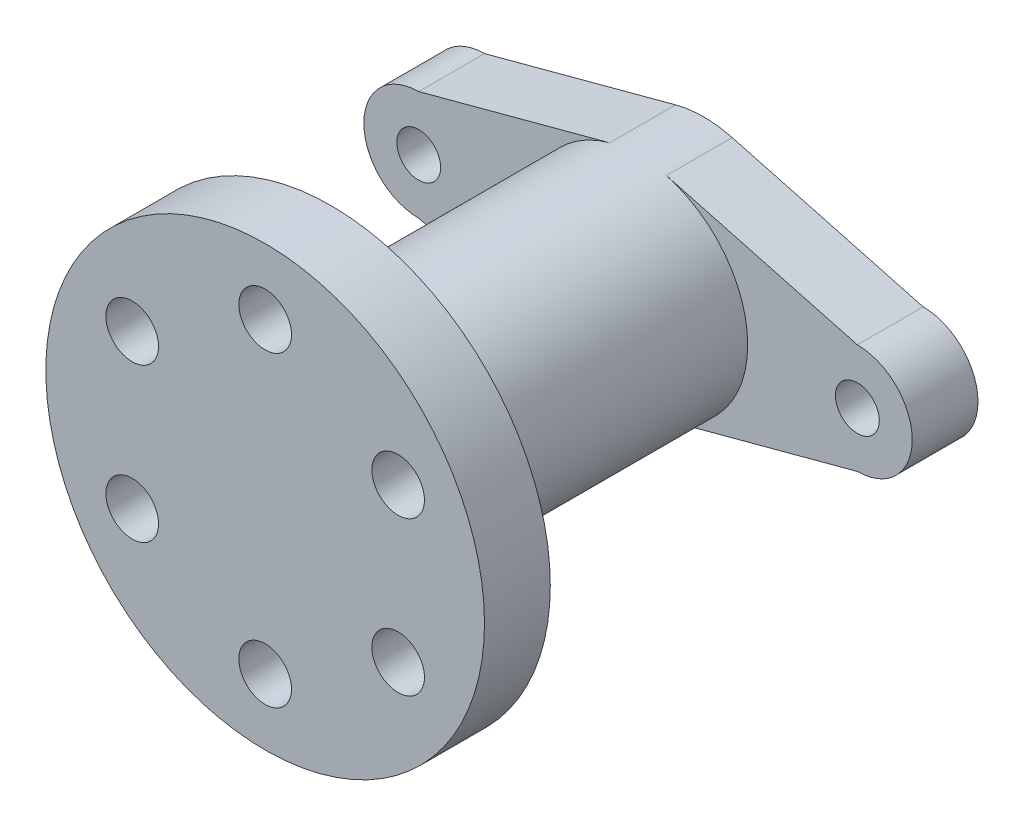
SolidWorks part; units mm, degrees
ref_plane "Front Plane" through (0, 0, 0) normal (0, 0, 1) x (1, 0, 0)
ref_plane "Top Plane" through (0, 0, 0) normal (0, 1, 0) x (1, 0, 0)
ref_plane "Right Plane" through (0, 0, 0) normal (1, 0, 0) x (0, 0, -1)
sketch "Sketch1" plane through (0, 0, 0) normal (0, 0, 1) x (1, 0, 0)
  line L0 (0, 125.6714) -> (0, -128.0999) construction
  line L1 (-233.9391, 0) -> (214.9164, 0) construction
  circle A0 centre (0, 0) radius 50
  dimension "D1" = 100
extrude "Boss-Extrude1" add sketch "Sketch1" along normal blind 15
sketch "Sketch2" plane through (0, 0, 0) normal (0, 0, -1) x (-1, 0, 0)
  circle A0 centre (0, 0) radius 25
  dimension "D1" = 50
extrude "Boss-Extrude2" add sketch "Sketch2" along normal blind 70
sketch "Sketch4" plane through (0, 0, -70) normal (0, 0, -1) x (-1, 0, 0)
  line L0 (0, 106.939) -> (0, 25) construction
  line L1 (-143.3635, 0) -> (-50, 0) construction
  line L2 (-50, 12.5) -> (-50, -95.9752) construction
  line L4 (-50, 12.5) -> (-6.4624, 24.1503)
  line L5 (50, 12.5) -> (6.4624, 24.1503)
  line L6 (-50, -12.5) -> (-6.4624, -24.1503)
  line L7 (50, -12.5) -> (6.4624, -24.1503)
  line L9 (0, -25) -> (0, -95.9752) construction
  line L10 (0, 106.939) -> (0, -95.9752) construction
  line L11 (-50, 106.939) -> (-50, -95.9752) construction
  arc A0 (-6.4624, -24.1503) -> (6.4624, -24.1503) centre (0, 0) ccw
  arc A1 (50, -12.5) -> (50, 12.5) centre (50, 0) ccw
  arc A2 (-50, -12.5) -> (-50, 12.5) centre (-50, 0) cw
  arc A3 (6.4624, 24.1503) -> (-6.4624, 24.1503) centre (0, 0) ccw
  dimension "D4" = 25
  dimension "D2" = 50
extrude "Boss-Extrude3" add sketch "Sketch4" along normal blind 15
sketch "Sketch5" plane through (0, 0, -85) normal (0, 0, -1) x (-1, 0, 0)
  circle A0 centre (0, 0) radius 15
  dimension "D1" = 30
extrude "Cut-Extrude1" cut sketch "Sketch5" against normal blind 85 contours A0
sketch "Sketch6" plane through (0, 0, -85) normal (0, 0, -1) x (-1, 0, 0)
  line L0 (0, 80.3656) -> (0, -80.9469) construction
  circle A0 centre (50, 0) radius 5
  circle A1 centre (-50, 0) radius 5
  dimension "D1" = 10
extrude "Cut-Extrude2" cut sketch "Sketch6" against normal blind 30
sketch "Sketch7" plane through (0, 0, 0) normal (0, 0, -1) x (-1, 0, 0)
  circle A0 centre (0, 0) radius 35 construction
  circle A1 centre (0, 35) radius 6
  circle A2 centre (30.3109, 17.5) radius 6
  circle A3 centre (30.3109, -17.5) radius 6
  circle A4 centre (0, -35) radius 6
  circle A5 centre (-30.3109, -17.5) radius 6
  circle A6 centre (-30.3109, 17.5) radius 6
  point P17 (0, 0)
  dimension "D1" = 70
  dimension "D2" = 12
  dimension "D3" = 6
extrude "Cut-Extrude3" cut sketch "Sketch7" against normal blind 30
